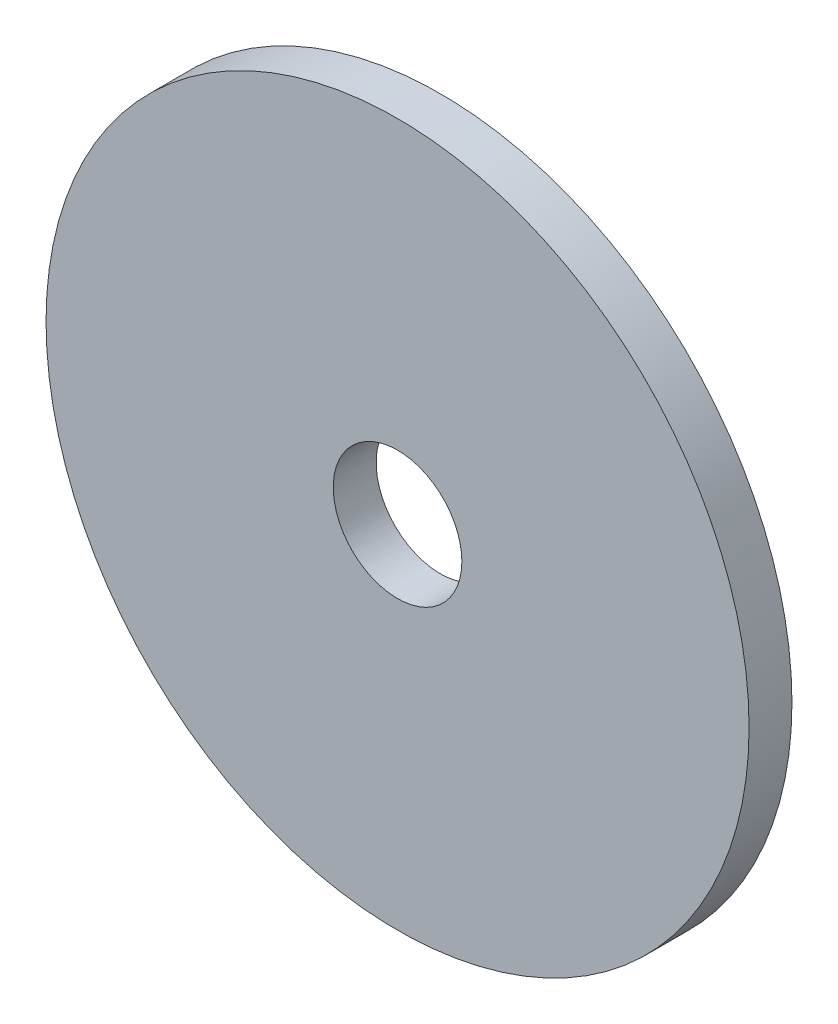
SolidWorks part; units mm, degrees
ref_plane "Plan de face" through (0, 0, 0) normal (0, 0, 1) x (1, 0, 0)
ref_plane "Plan de dessus" through (0, 0, 0) normal (0, 1, 0) x (1, 0, 0)
ref_plane "Plan de droite" through (0, 0, 0) normal (1, 0, 0) x (0, 0, -1)
sketch "Esquisse1" plane through (0, 0, 0) normal (0, 0, 1) x (1, 0, 0)
  circle A0 centre (0, 0) radius 16.4
  dimension "D1" = 32.8
extrude "Boss.-Extru.1" add sketch "Esquisse1" along normal blind 2
sketch "Esquisse3" plane through (0, 0, 2) normal (0, 0, 1) x (1, 0, 0)
  circle A0 centre (0, 0) radius 3
  dimension "D1" = 6
extrude "Enlèv. mat.-Extru.1" cut sketch "Esquisse3" against normal through all
